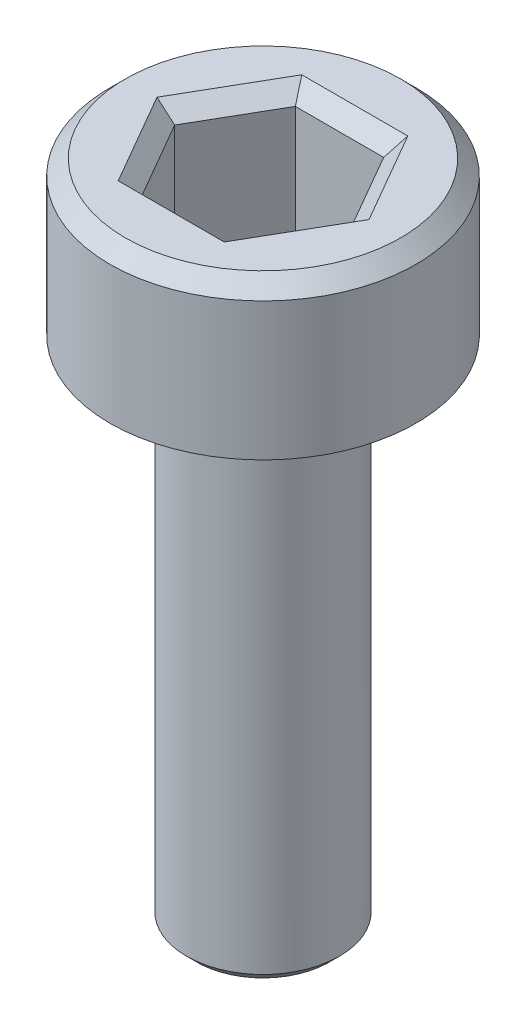
SolidWorks part; units mm, degrees
ref_plane "Front Plane" through (0, 0, 0) normal (0, 0, 1) x (1, 0, 0)
ref_plane "Top Plane" through (0, 0, 0) normal (0, 1, 0) x (1, 0, 0)
ref_plane "Right Plane" through (0, 0, 0) normal (1, 0, 0) x (0, 0, -1)
sketch "Sketch1" plane through (0, 0, 0) normal (0, 1, 0) x (1, 0, 0)
  circle A0 centre (0, 0) radius 3
  dimension "D1" = 6
extrude "Boss-Extrude1" add sketch "Sketch1" along normal blind 3
chamfer "Chamfer1" distance 0.3 angle 45 1 edges at (0, 3, 3)
sketch "Sketch2" plane through (0, 3, 0) normal (0, 1, 0) x (1, 0, 0)
  line L1 (1.7321, 0) -> (0.866, 1.5)
  line L2 (0.866, 1.5) -> (-0.866, 1.5)
  line L3 (-0.866, 1.5) -> (-1.7321, 0)
  line L4 (-1.7321, 0) -> (-0.866, -1.5)
  line L5 (-0.866, -1.5) -> (0.866, -1.5)
  line L6 (0.866, -1.5) -> (1.7321, 0)
  circle A0 centre (0, 0) radius 1.5 construction
  dimension "D1" = 3
extrude "Cut-Extrude1" cut sketch "Sketch2" against normal blind 2.5
chamfer "Chamfer2" distance 0.3 angle 45 6 edges at (1.299, 3, -0.75) (1.299, 3, 0.75) (0, 3, 1.5) (-1.299, 3, 0.75) (-1.299, 3, -0.75) (0, 3, -1.5)
sketch "Sketch3" plane through (0, 0, 0) normal (0, -1, 0) x (1, 0, 0)
  circle A0 centre (0, 0) radius 1.5
  dimension "D1" = 3
extrude "Boss-Extrude2" add sketch "Sketch3" along normal blind 10
chamfer "Chamfer3" distance 0.2 angle 45 1 edges at (0, -10, -1.5)
